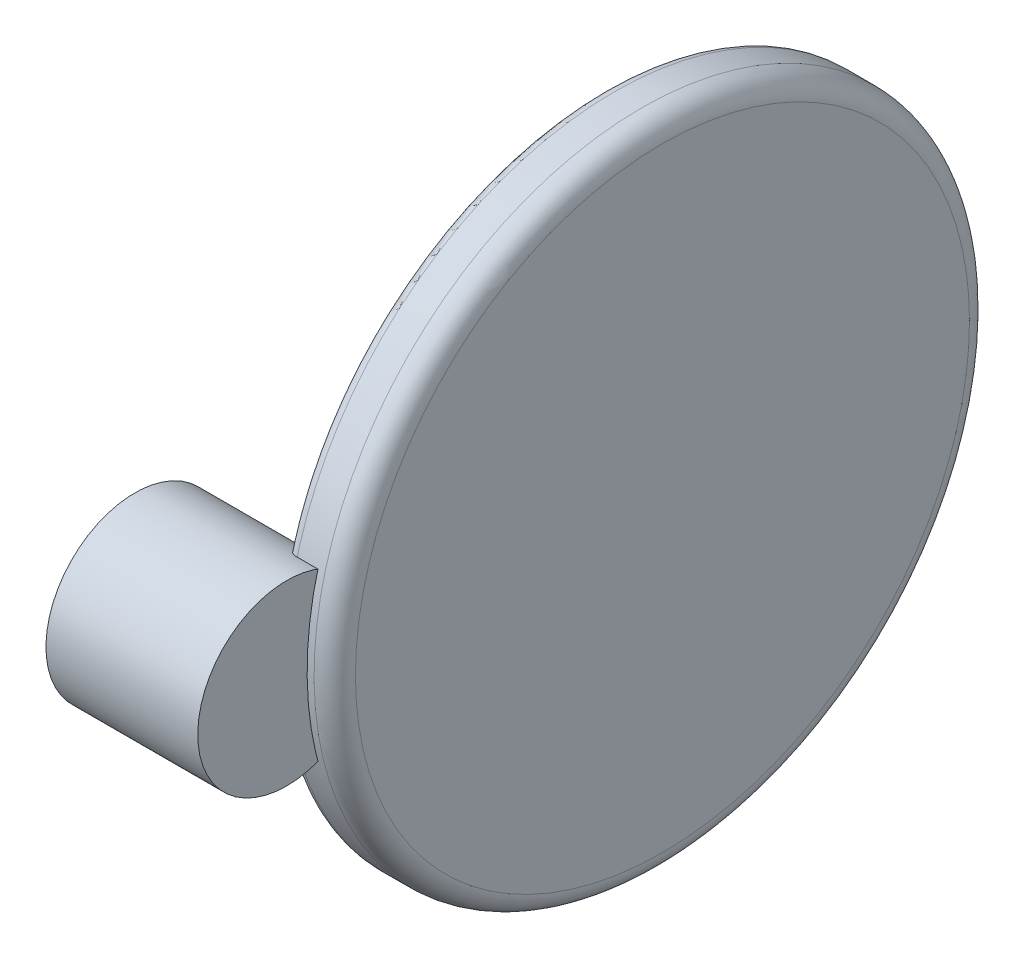
SolidWorks part; units mm, degrees
ref_plane "Front Plane" through (0, 0, 0) normal (0, 0, 1) x (1, 0, 0)
ref_plane "Top Plane" through (0, 0, 0) normal (0, 1, 0) x (1, 0, 0)
ref_plane "Right Plane" through (0, 0, 0) normal (1, 0, 0) x (0, 0, -1)
sketch "Sketch1" plane through (0, 0, 0) normal (0, 0, 1) x (1, 0, 0)
  line L0 (8.255, 0) -> (-8.255, 0) construction
  line L1 (30.255, 0) -> (-30.255, 0) construction
  line L2 (8.255, 0) -> (8.255, 12.9)
  line L3 (8.255, 12.9) -> (30.255, 12.9)
  line L4 (30.255, 12.9) -> (30.255, 0)
  line L5 (8.255, 0) -> (30.255, 0)
  point P4 (0, 0)
  point P8 (0, 0)
  dimension "D1" = 22
  dimension "D2" = 16.51
  dimension "D3" = 12.9
revolve "Revolve1" add sketch "Sketch1" angle 360 about L5
sketch "Sketch2" plane through (8.255, 0, 0) normal (-1, 0, 0) x (0, 0, 1)
  circle A0 centre (0, 0) radius 3.7138
  dimension "D1" = 7.4275
extrude "Cut-Extrude1" cut sketch "Sketch2" against normal blind 7.5725
sketch "Sketch3" plane through (30.255, 0, 0) normal (1, 0, 0) x (0, 0, -1)
  line L0 (-20.8953, -55) -> (-20.8953, -46.1532)
  line L1 (13.175, -55) -> (-13.175, -55) construction
  line L2 (13.175, -55) -> (13.175, 55) construction
  line L3 (13.175, 55) -> (-13.175, 55) construction
  line L4 (-13.175, -55) -> (-13.175, 55) construction
  line L5 (13.175, -55) -> (-13.175, 55) construction
  line L6 (13.175, 55) -> (-13.175, -55) construction
  line L7 (-24.3823, -32.1152) -> (-32.3245, -17.1152)
  line L9 (-5.4548, -55) -> (-5.4548, -44)
  line L11 (5.4547, -44) -> (5.4547, -55)
  line L12 (20.8953, -55) -> (20.8953, -46.1532)
  line L13 (24.3823, -32.1152) -> (32.3245, -17.1152)
  line L14 (12.1, 0) -> (-12.1, 0) construction
  line L15 (13.175, -55) -> (-13.175, 55) construction
  line L16 (13.175, 55) -> (-13.175, -55) construction
  line L17 (13.175, 55) -> (-13.175, 55) construction
  line L18 (24.3823, 32.1152) -> (32.3245, 17.1152)
  line L19 (20.8953, 55) -> (20.8953, 46.1532)
  line L20 (5.4547, 44) -> (5.4547, 55)
  line L21 (-5.4548, 55) -> (-5.4548, 44)
  line L22 (-24.3823, 32.1152) -> (-32.3245, 17.1152)
  line L23 (-20.8953, 55) -> (-20.8953, 46.1532)
  arc A15 (32.3245, -17.1152) -> (32.3245, 17.1152) centre (0, 0) ccw
  arc A16 (-5.4548, 55) -> (-20.8953, 55) centre (-13.175, 55) ccw
  arc A17 (-20.8953, -55) -> (-5.4548, -55) centre (-13.175, -55) ccw
  arc A18 (5.4547, -55) -> (20.8953, -55) centre (13.175, -55) ccw
  arc A19 (20.8953, 55) -> (5.4547, 55) centre (13.175, 55) ccw
  arc A20 (-5.4548, -44) -> (5.4547, -44) centre (0, -44) cw
  arc A21 (20.8953, -46.1532) -> (24.3823, -32.1152) centre (50.8953, -46.1532) cw
  arc A22 (-20.8953, -46.1532) -> (-24.3823, -32.1152) centre (-50.8953, -46.1532) ccw
  arc A23 (-20.8953, 46.1532) -> (-24.3823, 32.1152) centre (-50.8953, 46.1532) cw
  arc A24 (20.8953, 46.1532) -> (24.3823, 32.1152) centre (50.8953, 46.1532) ccw
  arc A25 (-5.4548, 44) -> (5.4547, 44) centre (0, 44) ccw
  arc A26 (5.4547, 55) -> (20.8953, 55) centre (13.175, 55) cw
  arc A27 (-20.8953, 55) -> (-5.4548, 55) centre (-13.175, 55) cw
  arc A29 (-32.3245, 17.1152) -> (-32.3245, -17.1152) centre (0, 0) ccw
  dimension "D3" = 15.4405
  dimension "D5" = 7.7203
  dimension "D4" = 30
  dimension "D7" = 15
  dimension "D9" = 110
  dimension "D1" = 73.152
  dimension "D6" = 15
  dimension "D2" = 26.35
  dimension "D8" = 11
sketch "Sketch4" plane through (30.255, 0, 0) normal (1, 0, 0) x (0, 0, -1)
  circle A0 centre (0, 0) radius 3.7138
  dimension "D1" = 7.4275
extrude "Cut-Extrude2" [suppressed] cut sketch "Sketch4" against normal blind 7.0725
move or copy body "Body-Move/Copy1" bodies to move or copy 102 copy yes number of copies 1 translate (0, 0, 50.4528)
sketch "Sketch5" plane through (0, 0, 0) normal (0, 0, 1) x (1, 0, 0)
  line L0 (8.255, 0) -> (34.255, 0) construction
  line L1 (8.255, 12.9) -> (8.255, -12.9) construction
  line L2 (34.255, 0) -> (25.755, 0) construction
  line L3 (34.255, 0) -> (34.255, 47.5)
  line L4 (34.255, 47.5) -> (25.755, 47.5)
  line L5 (25.755, 47.5) -> (25.755, 0)
  line L6 (34.255, 0) -> (25.755, 0)
  dimension "D1" = 26
  dimension "D2" = 8.5
  dimension "D3" = 47.5
revolve "Revolve2" add sketch "Sketch5" angle 360 about L6
fillet "Fillet1" radius 3 1 edges at (34.255, 47.5, 0)
fillet "Fillet2" radius 1.5 1 edges at (25.755, 47.5, 0)
